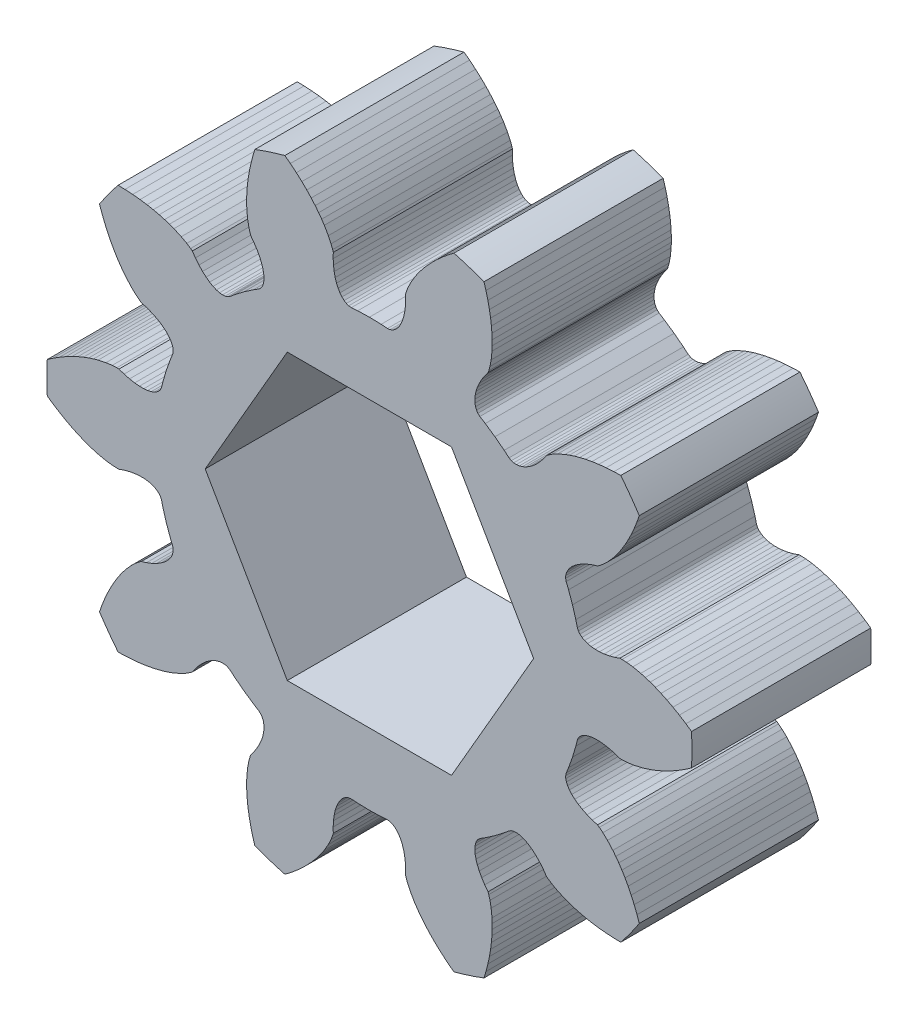
SolidWorks part; units mm, degrees
ref_plane "Front Plane" through (0, 0, 0) normal (0, 0, 1) x (1, 0, 0)
ref_plane "Top Plane" through (0, 0, 0) normal (0, 1, 0) x (1, 0, 0)
ref_plane "Right Plane" through (0, 0, 0) normal (1, 0, 0) x (0, 0, -1)
sketch "Model" plane through (0, 0, 0) normal (0, 0, 1) x (1, 0, 0)
  line L0 (8.9615, 5.6957) -> (8.8657, 5.453)
  line L1 (8.8657, 5.453) -> (8.7654, 5.2271)
  line L2 (8.7654, 5.2271) -> (8.663, 5.0202)
  line L3 (8.663, 5.0202) -> (8.5591, 4.8307)
  line L4 (8.5591, 4.8307) -> (8.454, 4.6566)
  line L5 (8.454, 4.6566) -> (8.3503, 4.5001)
  line L6 (8.3503, 4.5001) -> (8.2497, 4.3613)
  line L7 (8.2497, 4.3613) -> (8.1507, 4.2361)
  line L8 (8.1507, 4.2361) -> (7.9708, 4.0353)
  line L9 (7.9708, 4.0353) -> (7.8172, 3.8902)
  line L10 (7.8172, 3.8902) -> (7.6985, 3.7954)
  line L11 (7.6985, 3.7954) -> (7.6379, 3.7538)
  line L12 (7.6379, 3.7538) -> (7.4633, 3.7005)
  line L13 (7.4633, 3.7005) -> (7.288, 3.633)
  line L14 (7.288, 3.633) -> (7.1315, 3.5581)
  line L15 (7.1315, 3.5581) -> (6.994, 3.477)
  line L16 (6.994, 3.477) -> (6.8758, 3.3913)
  line L17 (6.8758, 3.3913) -> (6.7769, 3.3025)
  line L18 (6.7769, 3.3025) -> (6.6975, 3.212)
  line L19 (6.6975, 3.212) -> (6.6374, 3.1213)
  line L20 (6.6374, 3.1213) -> (6.5966, 3.0319)
  line L21 (6.5966, 3.0319) -> (6.5747, 2.9452)
  line L22 (6.5747, 2.9452) -> (6.5714, 2.8625)
  line L23 (6.5714, 2.8625) -> (6.5895, 2.7762)
  line L24 (6.5895, 2.7762) -> (6.6689, 2.5785)
  line L25 (6.6689, 2.5785) -> (6.8001, 2.2095)
  line L26 (6.8001, 2.2095) -> (6.9109, 1.8338)
  line L27 (6.9109, 1.8338) -> (6.9628, 1.6272)
  line L28 (6.9628, 1.6272) -> (6.9989, 1.5467)
  line L29 (6.9989, 1.5467) -> (7.0501, 1.4818)
  line L30 (7.0501, 1.4818) -> (7.1188, 1.4245)
  line L31 (7.1188, 1.4245) -> (7.2045, 1.3762)
  line L32 (7.2045, 1.3762) -> (7.3064, 1.3381)
  line L33 (7.3064, 1.3381) -> (7.4238, 1.3116)
  line L34 (7.4238, 1.3116) -> (7.556, 1.2978)
  line L35 (7.556, 1.2978) -> (7.702, 1.298)
  line L36 (7.702, 1.298) -> (7.8609, 1.3132)
  line L37 (7.8609, 1.3132) -> (8.0316, 1.3446)
  line L38 (8.0316, 1.3446) -> (8.2131, 1.3931)
  line L39 (8.2131, 1.3931) -> (8.3856, 1.4525)
  line L40 (8.3856, 1.4525) -> (8.4591, 1.4545)
  line L41 (8.4591, 1.4545) -> (8.6109, 1.4476)
  line L42 (8.6109, 1.4476) -> (8.8204, 1.4205)
  line L43 (8.8204, 1.4205) -> (9.0839, 1.3638)
  line L44 (9.0839, 1.3638) -> (9.2377, 1.3207)
  line L45 (9.2377, 1.3207) -> (9.4007, 1.2675)
  line L46 (9.4007, 1.2675) -> (9.5765, 1.2019)
  line L47 (9.5765, 1.2019) -> (9.7639, 1.1228)
  line L48 (9.7639, 1.1228) -> (9.9593, 1.0306)
  line L49 (9.9593, 1.0306) -> (10.1638, 0.9234)
  line L50 (10.1638, 0.9234) -> (10.3777, 0.7995)
  line L51 (10.3777, 0.7995) -> (10.5979, 0.6595)
  line L52 (10.5979, 0.6595) -> (10.787, 0.5284)
  line L53 (10.787, -0.5284) -> (10.5979, -0.6595)
  line L54 (10.5979, -0.6595) -> (10.3777, -0.7995)
  line L55 (10.3777, -0.7995) -> (10.1638, -0.9234)
  line L56 (10.1638, -0.9234) -> (9.9593, -1.0306)
  line L57 (9.9593, -1.0306) -> (9.7639, -1.1228)
  line L58 (9.7639, -1.1228) -> (9.5765, -1.2019)
  line L59 (9.5765, -1.2019) -> (9.4007, -1.2675)
  line L60 (9.4007, -1.2675) -> (9.2377, -1.3207)
  line L61 (9.2377, -1.3207) -> (9.0839, -1.3638)
  line L62 (9.0839, -1.3638) -> (8.8204, -1.4205)
  line L63 (8.8204, -1.4205) -> (8.6109, -1.4476)
  line L64 (8.6109, -1.4476) -> (8.4591, -1.4545)
  line L65 (8.4591, -1.4545) -> (8.3856, -1.4525)
  line L66 (8.3856, -1.4525) -> (8.2131, -1.3931)
  line L67 (8.2131, -1.3931) -> (8.0316, -1.3446)
  line L68 (8.0316, -1.3446) -> (7.8609, -1.3132)
  line L69 (7.8609, -1.3132) -> (7.702, -1.298)
  line L70 (7.702, -1.298) -> (7.556, -1.2978)
  line L71 (7.556, -1.2978) -> (7.4238, -1.3116)
  line L72 (7.4238, -1.3116) -> (7.3064, -1.3381)
  line L73 (7.3064, -1.3381) -> (7.2045, -1.3762)
  line L74 (7.2045, -1.3762) -> (7.1188, -1.4245)
  line L75 (7.1188, -1.4245) -> (7.0501, -1.4818)
  line L76 (7.0501, -1.4818) -> (6.9989, -1.5467)
  line L77 (6.9989, -1.5467) -> (6.9628, -1.6272)
  line L78 (6.9628, -1.6272) -> (6.9109, -1.8338)
  line L79 (6.9109, -1.8338) -> (6.8001, -2.2095)
  line L80 (6.8001, -2.2095) -> (6.6689, -2.5785)
  line L81 (6.6689, -2.5785) -> (6.5895, -2.7762)
  line L82 (6.5895, -2.7762) -> (6.5714, -2.8625)
  line L83 (6.5714, -2.8625) -> (6.5747, -2.9452)
  line L84 (6.5747, -2.9452) -> (6.5966, -3.0319)
  line L85 (6.5966, -3.0319) -> (6.6374, -3.1213)
  line L86 (6.6374, -3.1213) -> (6.6975, -3.212)
  line L87 (6.6975, -3.212) -> (6.7769, -3.3025)
  line L88 (6.7769, -3.3025) -> (6.8758, -3.3913)
  line L89 (6.8758, -3.3913) -> (6.994, -3.477)
  line L90 (6.994, -3.477) -> (7.1315, -3.5581)
  line L91 (7.1315, -3.5581) -> (7.288, -3.633)
  line L92 (7.288, -3.633) -> (7.4633, -3.7005)
  line L93 (7.4633, -3.7005) -> (7.6379, -3.7538)
  line L94 (7.6379, -3.7538) -> (7.6985, -3.7954)
  line L95 (7.6985, -3.7954) -> (7.8172, -3.8902)
  line L96 (7.8172, -3.8902) -> (7.9708, -4.0353)
  line L97 (7.9708, -4.0353) -> (8.1507, -4.2361)
  line L98 (8.1507, -4.2361) -> (8.2497, -4.3613)
  line L99 (8.2497, -4.3613) -> (8.3503, -4.5001)
  line L100 (8.3503, -4.5001) -> (8.454, -4.6566)
  line L101 (8.454, -4.6566) -> (8.5591, -4.8307)
  line L102 (8.5591, -4.8307) -> (8.663, -5.0202)
  line L103 (8.663, -5.0202) -> (8.7654, -5.2271)
  line L104 (8.7654, -5.2271) -> (8.8657, -5.453)
  line L105 (8.8657, -5.453) -> (8.9615, -5.6957)
  line L106 (8.9615, -5.6957) -> (9.0375, -5.9129)
  line L107 (8.4163, -6.768) -> (8.1862, -6.7628)
  line L108 (8.1862, -6.7628) -> (7.9258, -6.7467)
  line L109 (7.9258, -6.7467) -> (7.6799, -6.7211)
  line L110 (7.6799, -6.7211) -> (7.4515, -6.6877)
  line L111 (7.4515, -6.6877) -> (7.2392, -6.6474)
  line L112 (7.2392, -6.6474) -> (7.0411, -6.6013)
  line L113 (7.0411, -6.6013) -> (6.8603, -6.551)
  line L114 (6.8603, -6.551) -> (6.6971, -6.4982)
  line L115 (6.6971, -6.4982) -> (6.5474, -6.4428)
  line L116 (6.5474, -6.4428) -> (6.3009, -6.3337)
  line L117 (6.3009, -6.3337) -> (6.1155, -6.2324)
  line L118 (6.1155, -6.2324) -> (5.9886, -6.1488)
  line L119 (5.9886, -6.1488) -> (5.9304, -6.1041)
  line L120 (5.9304, -6.1041) -> (5.8257, -5.9545)
  line L121 (5.8257, -5.9545) -> (5.7074, -5.8087)
  line L122 (5.7074, -5.8087) -> (5.5877, -5.6829)
  line L123 (5.5877, -5.6829) -> (5.4681, -5.5772)
  line L124 (5.4681, -5.5772) -> (5.3501, -5.4912)
  line L125 (5.3501, -5.4912) -> (5.2351, -5.4247)
  line L126 (5.2351, -5.4247) -> (5.1245, -5.3771)
  line L127 (5.1245, -5.3771) -> (5.0197, -5.348)
  line L128 (5.0197, -5.348) -> (4.922, -5.3368)
  line L129 (4.922, -5.3368) -> (4.8327, -5.3428)
  line L130 (4.8327, -5.3428) -> (4.7531, -5.3652)
  line L131 (4.7531, -5.3652) -> (4.6766, -5.4091)
  line L132 (4.6766, -5.4091) -> (4.5131, -5.5457)
  line L133 (4.5131, -5.5457) -> (4.2027, -5.7845)
  line L134 (4.2027, -5.7845) -> (3.8796, -6.0059)
  line L135 (3.8796, -6.0059) -> (3.6992, -6.1192)
  line L136 (3.6992, -6.1192) -> (3.6338, -6.1784)
  line L137 (3.6338, -6.1784) -> (3.5879, -6.2472)
  line L138 (3.5879, -6.2472) -> (3.5546, -6.3302)
  line L139 (3.5546, -6.3302) -> (3.5351, -6.4266)
  line L140 (3.5351, -6.4266) -> (3.5304, -6.5353)
  line L141 (3.5304, -6.5353) -> (3.5415, -6.6552)
  line L142 (3.5415, -6.6552) -> (3.5692, -6.7851)
  line L143 (3.5692, -6.7851) -> (3.6145, -6.9239)
  line L144 (3.6145, -6.9239) -> (3.6781, -7.0703)
  line L145 (3.6781, -7.0703) -> (3.7607, -7.223)
  line L146 (3.7607, -7.223) -> (3.8629, -7.3806)
  line L147 (3.8629, -7.3806) -> (3.9727, -7.5264)
  line L148 (3.9727, -7.5264) -> (3.9973, -7.5956)
  line L149 (3.9973, -7.5956) -> (4.0376, -7.7421)
  line L150 (4.0376, -7.7421) -> (4.0766, -7.9498)
  line L151 (4.0766, -7.9498) -> (4.1042, -8.2179)
  line L152 (4.1042, -8.2179) -> (4.1107, -8.3774)
  line L153 (4.1107, -8.3774) -> (4.1104, -8.5489)
  line L154 (4.1104, -8.5489) -> (4.1024, -8.7364)
  line L155 (4.1024, -8.7364) -> (4.0851, -8.939)
  line L156 (4.0851, -8.939) -> (4.0577, -9.1534)
  line L157 (4.0577, -9.1534) -> (4.019, -9.381)
  line L158 (4.019, -9.381) -> (3.9673, -9.6227)
  line L159 (3.9673, -9.6227) -> (3.9022, -9.8754)
  line L160 (3.9022, -9.8754) -> (3.8359, -10.0957)
  line L161 (2.8308, -10.4223) -> (2.6477, -10.283)
  line L162 (2.6477, -10.283) -> (2.4465, -10.1169)
  line L163 (2.4465, -10.1169) -> (2.2626, -9.9517)
  line L164 (2.2626, -9.9517) -> (2.0975, -9.7903)
  line L165 (2.0975, -9.7903) -> (1.9493, -9.633)
  line L166 (1.9493, -9.633) -> (1.8163, -9.4792)
  line L167 (1.8163, -9.4792) -> (1.6995, -9.3323)
  line L168 (1.6995, -9.3323) -> (1.5985, -9.1937)
  line L169 (1.5985, -9.1937) -> (1.51, -9.0608)
  line L170 (1.51, -9.0608) -> (1.3747, -8.8277)
  line L171 (1.3747, -8.8277) -> (1.2842, -8.6367)
  line L172 (1.2842, -8.6367) -> (1.2307, -8.4945)
  line L173 (1.2307, -8.4945) -> (1.2099, -8.4241)
  line L174 (1.2099, -8.4241) -> (1.2131, -8.2416)
  line L175 (1.2131, -8.2416) -> (1.2031, -8.054)
  line L176 (1.2031, -8.054) -> (1.1802, -7.8819)
  line L177 (1.1802, -7.8819) -> (1.1456, -7.7261)
  line L178 (1.1456, -7.7261) -> (1.1006, -7.5872)
  line L179 (1.1006, -7.5872) -> (1.0467, -7.4658)
  line L180 (1.0467, -7.4658) -> (0.9852, -7.3623)
  line L181 (0.9852, -7.3623) -> (0.9175, -7.2771)
  line L182 (0.9175, -7.2771) -> (0.8451, -7.2106)
  line L183 (0.8451, -7.2106) -> (0.7693, -7.163)
  line L184 (0.7693, -7.163) -> (0.6917, -7.1343)
  line L185 (0.6917, -7.1343) -> (0.6041, -7.1249)
  line L186 (0.6041, -7.1249) -> (0.3915, -7.1393)
  line L187 (0.3915, -7.1393) -> (0, -7.15)
  line L188 (0, -7.15) -> (-0.3915, -7.1393)
  line L189 (-0.3915, -7.1393) -> (-0.6041, -7.1249)
  line L190 (-0.6041, -7.1249) -> (-0.6917, -7.1343)
  line L191 (-0.6917, -7.1343) -> (-0.7693, -7.163)
  line L192 (-0.7693, -7.163) -> (-0.8451, -7.2106)
  line L193 (-0.8451, -7.2106) -> (-0.9175, -7.2771)
  line L194 (-0.9175, -7.2771) -> (-0.9852, -7.3623)
  line L195 (-0.9852, -7.3623) -> (-1.0467, -7.4658)
  line L196 (-1.0467, -7.4658) -> (-1.1006, -7.5872)
  line L197 (-1.1006, -7.5872) -> (-1.1456, -7.7261)
  line L198 (-1.1456, -7.7261) -> (-1.1802, -7.8819)
  line L199 (-1.1802, -7.8819) -> (-1.2031, -8.054)
  line L200 (-1.2031, -8.054) -> (-1.2131, -8.2416)
  line L201 (-1.2131, -8.2416) -> (-1.2099, -8.4241)
  line L202 (-1.2099, -8.4241) -> (-1.2307, -8.4945)
  line L203 (-1.2307, -8.4945) -> (-1.2842, -8.6367)
  line L204 (-1.2842, -8.6367) -> (-1.3747, -8.8277)
  line L205 (-1.3747, -8.8277) -> (-1.51, -9.0608)
  line L206 (-1.51, -9.0608) -> (-1.5985, -9.1937)
  line L207 (-1.5985, -9.1937) -> (-1.6995, -9.3323)
  line L208 (-1.6995, -9.3323) -> (-1.8163, -9.4792)
  line L209 (-1.8163, -9.4792) -> (-1.9493, -9.633)
  line L210 (-1.9493, -9.633) -> (-2.0975, -9.7903)
  line L211 (-2.0975, -9.7903) -> (-2.2626, -9.9517)
  line L212 (-2.2626, -9.9517) -> (-2.4465, -10.1169)
  line L213 (-2.4465, -10.1169) -> (-2.6477, -10.283)
  line L214 (-2.6477, -10.283) -> (-2.8308, -10.4223)
  line L215 (-3.8359, -10.0957) -> (-3.9022, -9.8754)
  line L216 (-3.9022, -9.8754) -> (-3.9673, -9.6227)
  line L217 (-3.9673, -9.6227) -> (-4.019, -9.381)
  line L218 (-4.019, -9.381) -> (-4.0577, -9.1534)
  line L219 (-4.0577, -9.1534) -> (-4.0851, -8.939)
  line L220 (-4.0851, -8.939) -> (-4.1024, -8.7364)
  line L221 (-4.1024, -8.7364) -> (-4.1104, -8.5489)
  line L222 (-4.1104, -8.5489) -> (-4.1107, -8.3774)
  line L223 (-4.1107, -8.3774) -> (-4.1042, -8.2179)
  line L224 (-4.1042, -8.2179) -> (-4.0766, -7.9498)
  line L225 (-4.0766, -7.9498) -> (-4.0376, -7.7421)
  line L226 (-4.0376, -7.7421) -> (-3.9973, -7.5956)
  line L227 (-3.9973, -7.5956) -> (-3.9727, -7.5264)
  line L228 (-3.9727, -7.5264) -> (-3.8629, -7.3806)
  line L229 (-3.8629, -7.3806) -> (-3.7607, -7.223)
  line L230 (-3.7607, -7.223) -> (-3.6781, -7.0703)
  line L231 (-3.6781, -7.0703) -> (-3.6145, -6.9239)
  line L232 (-3.6145, -6.9239) -> (-3.5692, -6.7851)
  line L233 (-3.5692, -6.7851) -> (-3.5415, -6.6552)
  line L234 (-3.5415, -6.6552) -> (-3.5304, -6.5353)
  line L235 (-3.5304, -6.5353) -> (-3.5351, -6.4266)
  line L236 (-3.5351, -6.4266) -> (-3.5546, -6.3302)
  line L237 (-3.5546, -6.3302) -> (-3.5879, -6.2472)
  line L238 (-3.5879, -6.2472) -> (-3.6338, -6.1784)
  line L239 (-3.6338, -6.1784) -> (-3.6992, -6.1192)
  line L240 (-3.6992, -6.1192) -> (-3.8796, -6.0059)
  line L241 (-3.8796, -6.0059) -> (-4.2027, -5.7845)
  line L242 (-4.2027, -5.7845) -> (-4.5131, -5.5457)
  line L243 (-4.5131, -5.5457) -> (-4.6766, -5.4091)
  line L244 (-4.6766, -5.4091) -> (-4.7531, -5.3652)
  line L245 (-4.7531, -5.3652) -> (-4.8327, -5.3428)
  line L246 (-4.8327, -5.3428) -> (-4.922, -5.3368)
  line L247 (-4.922, -5.3368) -> (-5.0197, -5.348)
  line L248 (-5.0197, -5.348) -> (-5.1245, -5.3771)
  line L249 (-5.1245, -5.3771) -> (-5.2351, -5.4247)
  line L250 (-5.2351, -5.4247) -> (-5.3501, -5.4912)
  line L251 (-5.3501, -5.4912) -> (-5.4681, -5.5772)
  line L252 (-5.4681, -5.5772) -> (-5.5877, -5.6829)
  line L253 (-5.5877, -5.6829) -> (-5.7074, -5.8087)
  line L254 (-5.7074, -5.8087) -> (-5.8257, -5.9545)
  line L255 (-5.8257, -5.9545) -> (-5.9304, -6.1041)
  line L256 (-5.9304, -6.1041) -> (-5.9886, -6.1488)
  line L257 (-5.9886, -6.1488) -> (-6.1155, -6.2324)
  line L258 (-6.1155, -6.2324) -> (-6.3009, -6.3337)
  line L259 (-6.3009, -6.3337) -> (-6.5474, -6.4428)
  line L260 (-6.5474, -6.4428) -> (-6.6971, -6.4982)
  line L261 (-6.6971, -6.4982) -> (-6.8603, -6.551)
  line L262 (-6.8603, -6.551) -> (-7.0411, -6.6013)
  line L263 (-7.0411, -6.6013) -> (-7.2392, -6.6474)
  line L264 (-7.2392, -6.6474) -> (-7.4515, -6.6877)
  line L265 (-7.4515, -6.6877) -> (-7.6799, -6.7211)
  line L266 (-7.6799, -6.7211) -> (-7.9258, -6.7467)
  line L267 (-7.9258, -6.7467) -> (-8.1862, -6.7628)
  line L268 (-8.1862, -6.7628) -> (-8.4163, -6.768)
  line L269 (-9.0375, -5.9129) -> (-8.9615, -5.6957)
  line L270 (-8.9615, -5.6957) -> (-8.8657, -5.453)
  line L271 (-8.8657, -5.453) -> (-8.7654, -5.2271)
  line L272 (-8.7654, -5.2271) -> (-8.663, -5.0202)
  line L273 (-8.663, -5.0202) -> (-8.5591, -4.8307)
  line L274 (-8.5591, -4.8307) -> (-8.454, -4.6566)
  line L275 (-8.454, -4.6566) -> (-8.3503, -4.5001)
  line L276 (-8.3503, -4.5001) -> (-8.2497, -4.3613)
  line L277 (-8.2497, -4.3613) -> (-8.1507, -4.2361)
  line L278 (-8.1507, -4.2361) -> (-7.9708, -4.0353)
  line L279 (-7.9708, -4.0353) -> (-7.8172, -3.8902)
  line L280 (-7.8172, -3.8902) -> (-7.6985, -3.7954)
  line L281 (-7.6985, -3.7954) -> (-7.6379, -3.7538)
  line L282 (-7.6379, -3.7538) -> (-7.4633, -3.7005)
  line L283 (-7.4633, -3.7005) -> (-7.288, -3.633)
  line L284 (-7.288, -3.633) -> (-7.1315, -3.5581)
  line L285 (-7.1315, -3.5581) -> (-6.994, -3.477)
  line L286 (-6.994, -3.477) -> (-6.8758, -3.3913)
  line L287 (-6.8758, -3.3913) -> (-6.7769, -3.3025)
  line L288 (-6.7769, -3.3025) -> (-6.6975, -3.212)
  line L289 (-6.6975, -3.212) -> (-6.6374, -3.1213)
  line L290 (-6.6374, -3.1213) -> (-6.5966, -3.0319)
  line L291 (-6.5966, -3.0319) -> (-6.5747, -2.9452)
  line L292 (-6.5747, -2.9452) -> (-6.5714, -2.8625)
  line L293 (-6.5714, -2.8625) -> (-6.5895, -2.7762)
  line L294 (-6.5895, -2.7762) -> (-6.6689, -2.5785)
  line L295 (-6.6689, -2.5785) -> (-6.8001, -2.2095)
  line L296 (-6.8001, -2.2095) -> (-6.9109, -1.8338)
  line L297 (-6.9109, -1.8338) -> (-6.9628, -1.6272)
  line L298 (-6.9628, -1.6272) -> (-6.9989, -1.5467)
  line L299 (-6.9989, -1.5467) -> (-7.0501, -1.4818)
  line L300 (-7.0501, -1.4818) -> (-7.1188, -1.4245)
  line L301 (-7.1188, -1.4245) -> (-7.2045, -1.3762)
  line L302 (-7.2045, -1.3762) -> (-7.3064, -1.3381)
  line L303 (-7.3064, -1.3381) -> (-7.4238, -1.3116)
  line L304 (-7.4238, -1.3116) -> (-7.556, -1.2978)
  line L305 (-7.556, -1.2978) -> (-7.702, -1.298)
  line L306 (-7.702, -1.298) -> (-7.8609, -1.3132)
  line L307 (-7.8609, -1.3132) -> (-8.0316, -1.3446)
  line L308 (-8.0316, -1.3446) -> (-8.2131, -1.3931)
  line L309 (-8.2131, -1.3931) -> (-8.3856, -1.4525)
  line L310 (-8.3856, -1.4525) -> (-8.4591, -1.4545)
  line L311 (-8.4591, -1.4545) -> (-8.6109, -1.4476)
  line L312 (-8.6109, -1.4476) -> (-8.8204, -1.4205)
  line L313 (-8.8204, -1.4205) -> (-9.0839, -1.3638)
  line L314 (-9.0839, -1.3638) -> (-9.2377, -1.3207)
  line L315 (-9.2377, -1.3207) -> (-9.4007, -1.2675)
  line L316 (-9.4007, -1.2675) -> (-9.5765, -1.2019)
  line L317 (-9.5765, -1.2019) -> (-9.7639, -1.1228)
  line L318 (-9.7639, -1.1228) -> (-9.9593, -1.0306)
  line L319 (-9.9593, -1.0306) -> (-10.1638, -0.9234)
  line L320 (-10.1638, -0.9234) -> (-10.3777, -0.7995)
  line L321 (-10.3777, -0.7995) -> (-10.5979, -0.6595)
  line L322 (-10.5979, -0.6595) -> (-10.787, -0.5284)
  line L323 (-10.787, 0.5284) -> (-10.5979, 0.6595)
  line L324 (-10.5979, 0.6595) -> (-10.3777, 0.7995)
  line L325 (-10.3777, 0.7995) -> (-10.1638, 0.9234)
  line L326 (-10.1638, 0.9234) -> (-9.9593, 1.0306)
  line L327 (-9.9593, 1.0306) -> (-9.7639, 1.1228)
  line L328 (-9.7639, 1.1228) -> (-9.5765, 1.2019)
  line L329 (-9.5765, 1.2019) -> (-9.4007, 1.2675)
  line L330 (-9.4007, 1.2675) -> (-9.2377, 1.3207)
  line L331 (-9.2377, 1.3207) -> (-9.0839, 1.3638)
  line L332 (-9.0839, 1.3638) -> (-8.8204, 1.4205)
  line L333 (-8.8204, 1.4205) -> (-8.6109, 1.4476)
  line L334 (-8.6109, 1.4476) -> (-8.4591, 1.4545)
  line L335 (-8.4591, 1.4545) -> (-8.3856, 1.4525)
  line L336 (-8.3856, 1.4525) -> (-8.2131, 1.3931)
  line L337 (-8.2131, 1.3931) -> (-8.0316, 1.3446)
  line L338 (-8.0316, 1.3446) -> (-7.8609, 1.3132)
  line L339 (-7.8609, 1.3132) -> (-7.702, 1.298)
  line L340 (-7.702, 1.298) -> (-7.556, 1.2978)
  line L341 (-7.556, 1.2978) -> (-7.4238, 1.3116)
  line L342 (-7.4238, 1.3116) -> (-7.3064, 1.3381)
  line L343 (-7.3064, 1.3381) -> (-7.2045, 1.3762)
  line L344 (-7.2045, 1.3762) -> (-7.1188, 1.4245)
  line L345 (-7.1188, 1.4245) -> (-7.0501, 1.4818)
  line L346 (-7.0501, 1.4818) -> (-6.9989, 1.5467)
  line L347 (-6.9989, 1.5467) -> (-6.9628, 1.6272)
  line L348 (-6.9628, 1.6272) -> (-6.9109, 1.8338)
  line L349 (-6.9109, 1.8338) -> (-6.8001, 2.2095)
  line L350 (-6.8001, 2.2095) -> (-6.6689, 2.5785)
  line L351 (-6.6689, 2.5785) -> (-6.5895, 2.7762)
  line L352 (-6.5895, 2.7762) -> (-6.5714, 2.8625)
  line L353 (-6.5714, 2.8625) -> (-6.5747, 2.9452)
  line L354 (-6.5747, 2.9452) -> (-6.5966, 3.0319)
  line L355 (-6.5966, 3.0319) -> (-6.6374, 3.1213)
  line L356 (-6.6374, 3.1213) -> (-6.6975, 3.212)
  line L357 (-6.6975, 3.212) -> (-6.7769, 3.3025)
  line L358 (-6.7769, 3.3025) -> (-6.8758, 3.3913)
  line L359 (-6.8758, 3.3913) -> (-6.994, 3.477)
  line L360 (-6.994, 3.477) -> (-7.1315, 3.5581)
  line L361 (-7.1315, 3.5581) -> (-7.288, 3.633)
  line L362 (-7.288, 3.633) -> (-7.4633, 3.7005)
  line L363 (-7.4633, 3.7005) -> (-7.6379, 3.7538)
  line L364 (-7.6379, 3.7538) -> (-7.6985, 3.7954)
  line L365 (-7.6985, 3.7954) -> (-7.8172, 3.8902)
  line L366 (-7.8172, 3.8902) -> (-7.9708, 4.0353)
  line L367 (-7.9708, 4.0353) -> (-8.1507, 4.2361)
  line L368 (-8.1507, 4.2361) -> (-8.2497, 4.3613)
  line L369 (-8.2497, 4.3613) -> (-8.3503, 4.5001)
  line L370 (-8.3503, 4.5001) -> (-8.454, 4.6566)
  line L371 (-8.454, 4.6566) -> (-8.5591, 4.8307)
  line L372 (-8.5591, 4.8307) -> (-8.663, 5.0202)
  line L373 (-8.663, 5.0202) -> (-8.7654, 5.2271)
  line L374 (-8.7654, 5.2271) -> (-8.8657, 5.453)
  line L375 (-8.8657, 5.453) -> (-8.9615, 5.6957)
  line L376 (-8.9615, 5.6957) -> (-9.0375, 5.9129)
  line L377 (-8.4163, 6.768) -> (-8.1862, 6.7628)
  line L378 (-8.1862, 6.7628) -> (-7.9258, 6.7467)
  line L379 (-7.9258, 6.7467) -> (-7.6799, 6.7211)
  line L380 (-7.6799, 6.7211) -> (-7.4515, 6.6877)
  line L381 (-7.4515, 6.6877) -> (-7.2392, 6.6474)
  line L382 (-7.2392, 6.6474) -> (-7.0411, 6.6013)
  line L383 (-7.0411, 6.6013) -> (-6.8603, 6.551)
  line L384 (-6.8603, 6.551) -> (-6.6971, 6.4982)
  line L385 (-6.6971, 6.4982) -> (-6.5474, 6.4428)
  line L386 (-6.5474, 6.4428) -> (-6.3009, 6.3337)
  line L387 (-6.3009, 6.3337) -> (-6.1155, 6.2324)
  line L388 (-6.1155, 6.2324) -> (-5.9886, 6.1488)
  line L389 (-5.9886, 6.1488) -> (-5.9304, 6.1041)
  line L390 (-5.9304, 6.1041) -> (-5.8257, 5.9545)
  line L391 (-5.8257, 5.9545) -> (-5.7074, 5.8087)
  line L392 (-5.7074, 5.8087) -> (-5.5877, 5.6829)
  line L393 (-5.5877, 5.6829) -> (-5.4681, 5.5772)
  line L394 (-5.4681, 5.5772) -> (-5.3501, 5.4912)
  line L395 (-5.3501, 5.4912) -> (-5.2351, 5.4247)
  line L396 (-5.2351, 5.4247) -> (-5.1245, 5.3771)
  line L397 (-5.1245, 5.3771) -> (-5.0197, 5.348)
  line L398 (-5.0197, 5.348) -> (-4.922, 5.3368)
  line L399 (-4.922, 5.3368) -> (-4.8327, 5.3428)
  line L400 (-4.8327, 5.3428) -> (-4.7531, 5.3652)
  line L401 (-4.7531, 5.3652) -> (-4.6766, 5.4091)
  line L402 (-4.6766, 5.4091) -> (-4.5131, 5.5457)
  line L403 (-4.5131, 5.5457) -> (-4.2027, 5.7845)
  line L404 (-4.2027, 5.7845) -> (-3.8796, 6.0059)
  line L405 (-3.8796, 6.0059) -> (-3.6992, 6.1192)
  line L406 (-3.6992, 6.1192) -> (-3.6338, 6.1784)
  line L407 (-3.6338, 6.1784) -> (-3.5879, 6.2472)
  line L408 (-3.5879, 6.2472) -> (-3.5546, 6.3302)
  line L409 (-3.5546, 6.3302) -> (-3.5351, 6.4266)
  line L410 (-3.5351, 6.4266) -> (-3.5304, 6.5353)
  line L411 (-3.5304, 6.5353) -> (-3.5415, 6.6552)
  line L412 (-3.5415, 6.6552) -> (-3.5692, 6.7851)
  line L413 (-3.5692, 6.7851) -> (-3.6145, 6.9239)
  line L414 (-3.6145, 6.9239) -> (-3.6781, 7.0703)
  line L415 (-3.6781, 7.0703) -> (-3.7607, 7.223)
  line L416 (-3.7607, 7.223) -> (-3.8629, 7.3806)
  line L417 (-3.8629, 7.3806) -> (-3.9727, 7.5264)
  line L418 (-3.9727, 7.5264) -> (-3.9973, 7.5956)
  line L419 (-3.9973, 7.5956) -> (-4.0376, 7.7421)
  line L420 (-4.0376, 7.7421) -> (-4.0766, 7.9498)
  line L421 (-4.0766, 7.9498) -> (-4.1042, 8.2179)
  line L422 (-4.1042, 8.2179) -> (-4.1107, 8.3774)
  line L423 (-4.1107, 8.3774) -> (-4.1104, 8.5489)
  line L424 (-4.1104, 8.5489) -> (-4.1024, 8.7364)
  line L425 (-4.1024, 8.7364) -> (-4.0851, 8.939)
  line L426 (-4.0851, 8.939) -> (-4.0577, 9.1534)
  line L427 (-4.0577, 9.1534) -> (-4.019, 9.381)
  line L428 (-4.019, 9.381) -> (-3.9673, 9.6227)
  line L429 (-3.9673, 9.6227) -> (-3.9022, 9.8754)
  line L430 (-3.9022, 9.8754) -> (-3.8359, 10.0957)
  line L431 (-2.8308, 10.4223) -> (-2.6477, 10.283)
  line L432 (-2.6477, 10.283) -> (-2.4465, 10.1169)
  line L433 (-2.4465, 10.1169) -> (-2.2626, 9.9517)
  line L434 (-2.2626, 9.9517) -> (-2.0975, 9.7903)
  line L435 (-2.0975, 9.7903) -> (-1.9493, 9.633)
  line L436 (-1.9493, 9.633) -> (-1.8163, 9.4792)
  line L437 (-1.8163, 9.4792) -> (-1.6995, 9.3323)
  line L438 (-1.6995, 9.3323) -> (-1.5985, 9.1937)
  line L439 (-1.5985, 9.1937) -> (-1.51, 9.0608)
  line L440 (-1.51, 9.0608) -> (-1.3747, 8.8277)
  line L441 (-1.3747, 8.8277) -> (-1.2842, 8.6367)
  line L442 (-1.2842, 8.6367) -> (-1.2307, 8.4945)
  line L443 (-1.2307, 8.4945) -> (-1.2099, 8.4241)
  line L444 (-1.2099, 8.4241) -> (-1.2131, 8.2416)
  line L445 (-1.2131, 8.2416) -> (-1.2031, 8.054)
  line L446 (-1.2031, 8.054) -> (-1.1802, 7.8819)
  line L447 (-1.1802, 7.8819) -> (-1.1456, 7.7261)
  line L448 (-1.1456, 7.7261) -> (-1.1006, 7.5872)
  line L449 (-1.1006, 7.5872) -> (-1.0467, 7.4658)
  line L450 (-1.0467, 7.4658) -> (-0.9852, 7.3623)
  line L451 (-0.9852, 7.3623) -> (-0.9175, 7.2771)
  line L452 (-0.9175, 7.2771) -> (-0.8451, 7.2106)
  line L453 (-0.8451, 7.2106) -> (-0.7693, 7.163)
  line L454 (-0.7693, 7.163) -> (-0.6917, 7.1343)
  line L455 (-0.6917, 7.1343) -> (-0.6041, 7.1249)
  line L456 (-0.6041, 7.1249) -> (-0.3915, 7.1393)
  line L457 (-0.3915, 7.1393) -> (0, 7.15)
  line L458 (0, 7.15) -> (0.3915, 7.1393)
  line L459 (0.3915, 7.1393) -> (0.6041, 7.1249)
  line L460 (0.6041, 7.1249) -> (0.6917, 7.1343)
  line L461 (0.6917, 7.1343) -> (0.7693, 7.163)
  line L462 (0.7693, 7.163) -> (0.8451, 7.2106)
  line L463 (0.8451, 7.2106) -> (0.9175, 7.2771)
  line L464 (0.9175, 7.2771) -> (0.9852, 7.3623)
  line L465 (0.9852, 7.3623) -> (1.0467, 7.4658)
  line L466 (1.0467, 7.4658) -> (1.1006, 7.5872)
  line L467 (1.1006, 7.5872) -> (1.1456, 7.7261)
  line L468 (1.1456, 7.7261) -> (1.1802, 7.8819)
  line L469 (1.1802, 7.8819) -> (1.2031, 8.054)
  line L470 (1.2031, 8.054) -> (1.2131, 8.2416)
  line L471 (1.2131, 8.2416) -> (1.2099, 8.4241)
  line L472 (1.2099, 8.4241) -> (1.2307, 8.4945)
  line L473 (1.2307, 8.4945) -> (1.2842, 8.6367)
  line L474 (1.2842, 8.6367) -> (1.3747, 8.8277)
  line L475 (1.3747, 8.8277) -> (1.51, 9.0608)
  line L476 (1.51, 9.0608) -> (1.5985, 9.1937)
  line L477 (1.5985, 9.1937) -> (1.6995, 9.3323)
  line L478 (1.6995, 9.3323) -> (1.8163, 9.4792)
  line L479 (1.8163, 9.4792) -> (1.9493, 9.633)
  line L480 (1.9493, 9.633) -> (2.0975, 9.7903)
  line L481 (2.0975, 9.7903) -> (2.2626, 9.9517)
  line L482 (2.2626, 9.9517) -> (2.4465, 10.1169)
  line L483 (2.4465, 10.1169) -> (2.6477, 10.283)
  line L484 (2.6477, 10.283) -> (2.8308, 10.4223)
  line L485 (3.8359, 10.0957) -> (3.9022, 9.8754)
  line L486 (3.9022, 9.8754) -> (3.9673, 9.6227)
  line L487 (3.9673, 9.6227) -> (4.019, 9.381)
  line L488 (4.019, 9.381) -> (4.0577, 9.1534)
  line L489 (4.0577, 9.1534) -> (4.0851, 8.939)
  line L490 (4.0851, 8.939) -> (4.1024, 8.7364)
  line L491 (4.1024, 8.7364) -> (4.1104, 8.5489)
  line L492 (4.1104, 8.5489) -> (4.1107, 8.3774)
  line L493 (4.1107, 8.3774) -> (4.1042, 8.2179)
  line L494 (4.1042, 8.2179) -> (4.0766, 7.9498)
  line L495 (4.0766, 7.9498) -> (4.0376, 7.7421)
  line L496 (4.0376, 7.7421) -> (3.9973, 7.5956)
  line L497 (3.9973, 7.5956) -> (3.9727, 7.5264)
  line L498 (3.9727, 7.5264) -> (3.8629, 7.3806)
  line L499 (3.8629, 7.3806) -> (3.7607, 7.223)
  line L500 (3.7607, 7.223) -> (3.6781, 7.0703)
  line L501 (3.6781, 7.0703) -> (3.6145, 6.9239)
  line L502 (3.6145, 6.9239) -> (3.5692, 6.7851)
  line L503 (3.5692, 6.7851) -> (3.5415, 6.6552)
  line L504 (3.5415, 6.6552) -> (3.5304, 6.5353)
  line L505 (3.5304, 6.5353) -> (3.5351, 6.4266)
  line L506 (3.5351, 6.4266) -> (3.5546, 6.3302)
  line L507 (3.5546, 6.3302) -> (3.5879, 6.2472)
  line L508 (3.5879, 6.2472) -> (3.6338, 6.1784)
  line L509 (3.6338, 6.1784) -> (3.6992, 6.1192)
  line L510 (3.6992, 6.1192) -> (3.8796, 6.0059)
  line L511 (3.8796, 6.0059) -> (4.2027, 5.7845)
  line L512 (4.2027, 5.7845) -> (4.5131, 5.5457)
  line L513 (4.5131, 5.5457) -> (4.6766, 5.4091)
  line L514 (4.6766, 5.4091) -> (4.7531, 5.3652)
  line L515 (4.7531, 5.3652) -> (4.8327, 5.3428)
  line L516 (4.8327, 5.3428) -> (4.922, 5.3368)
  line L517 (4.922, 5.3368) -> (5.0197, 5.348)
  line L518 (5.0197, 5.348) -> (5.1245, 5.3771)
  line L519 (5.1245, 5.3771) -> (5.2351, 5.4247)
  line L520 (5.2351, 5.4247) -> (5.3501, 5.4912)
  line L521 (5.3501, 5.4912) -> (5.4681, 5.5772)
  line L522 (5.4681, 5.5772) -> (5.5877, 5.6829)
  line L523 (5.5877, 5.6829) -> (5.7074, 5.8087)
  line L524 (5.7074, 5.8087) -> (5.8257, 5.9545)
  line L525 (5.8257, 5.9545) -> (5.9304, 6.1041)
  line L526 (5.9304, 6.1041) -> (5.9886, 6.1488)
  line L527 (5.9886, 6.1488) -> (6.1155, 6.2324)
  line L528 (6.1155, 6.2324) -> (6.3009, 6.3337)
  line L529 (6.3009, 6.3337) -> (6.5474, 6.4428)
  line L530 (6.5474, 6.4428) -> (6.6971, 6.4982)
  line L531 (6.6971, 6.4982) -> (6.8603, 6.551)
  line L532 (6.8603, 6.551) -> (7.0411, 6.6013)
  line L533 (7.0411, 6.6013) -> (7.2392, 6.6474)
  line L534 (7.2392, 6.6474) -> (7.4515, 6.6877)
  line L535 (7.4515, 6.6877) -> (7.6799, 6.7211)
  line L536 (7.6799, 6.7211) -> (7.9258, 6.7467)
  line L537 (7.9258, 6.7467) -> (8.1862, 6.7628)
  line L538 (8.1862, 6.7628) -> (8.4163, 6.768)
  line L539 (9.0375, 5.9129) -> (8.9615, 5.6957)
  line L541 (2.7497, 4.7624) -> (-2.7496, 4.7624)
  line L542 (-2.7496, 4.7624) -> (-5.4992, -0.0001)
  line L543 (-5.4992, -0.0001) -> (-2.7496, -4.7626)
  line L544 (-2.7496, -4.7626) -> (2.7497, -4.7626)
  line L545 (2.7497, -4.7626) -> (5.4993, -0.0001)
  line L546 (5.4993, -0.0001) -> (2.7497, 4.7624)
  arc A0 (10.787, -0.5284) -> (10.787, 0.5284) centre (-0.0001, 0) ccw
  arc A1 (8.4163, -6.768) -> (9.0375, -5.9129) centre (-0.0001, 0) ccw
  arc A2 (2.8308, -10.4223) -> (3.8359, -10.0957) centre (0, 0.0001) ccw
  arc A3 (-3.8359, -10.0957) -> (-2.8308, -10.4223) centre (0, 0.0001) ccw
  arc A4 (-9.0375, -5.9129) -> (-8.4163, -6.768) centre (0.0001, 0) ccw
  arc A5 (-10.787, 0.5284) -> (-10.787, -0.5284) centre (0.0001, 0) ccw
  arc A6 (-8.4163, 6.768) -> (-9.0375, 5.9129) centre (0.0001, 0) ccw
  arc A7 (-2.8308, 10.4223) -> (-3.8359, 10.0957) centre (0, -0.0001) ccw
  arc A8 (3.8359, 10.0957) -> (2.8308, 10.4223) centre (0, -0.0001) ccw
  arc A9 (9.0375, 5.9129) -> (8.4163, 6.768) centre (-0.0001, 0) ccw
  circle A10 centre (0, -0.0001) radius 4.7625 construction
  dimension "D1" = 10.8
  dimension "D2" = 9.525
extrude "Boss-Extrude1" add sketch "Model" along normal mid plane 6
